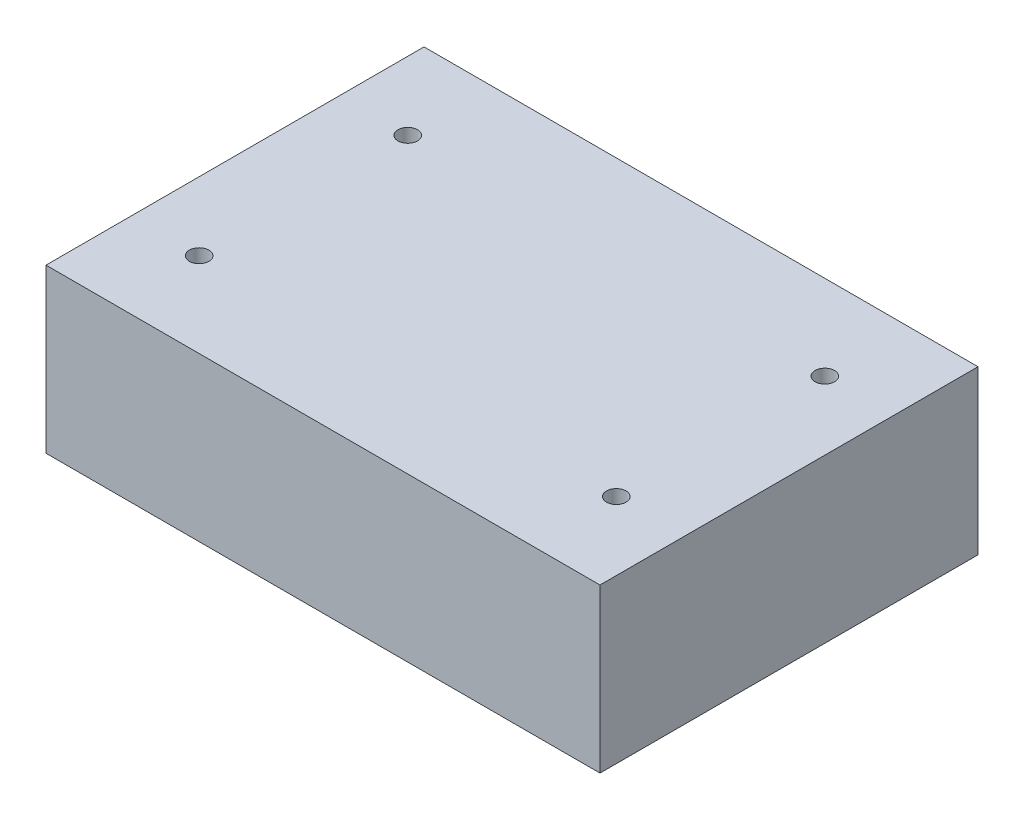
SolidWorks part; units mm, degrees
ref_plane "Front" through (0, 0, 0) normal (0, 0, 1) x (1, 0, 0)
ref_plane "Top" through (0, 0, 0) normal (0, 1, 0) x (1, 0, 0)
ref_plane "Right" through (0, 0, 0) normal (1, 0, 0) x (0, 0, -1)
sketch "Sketch1" plane through (0, 0, 0) normal (0, 1, 0) x (1, 0, 0)
  line L0 (0, 29) -> (85, 29) construction
  line L1 (0, 0) -> (85, 0)
  line L2 (0, 0) -> (0, 58)
  line L3 (0, 58) -> (85, 58)
  line L4 (85, 0) -> (85, 58)
  line L5 (42.5, 58) -> (42.5, 0) construction
  circle A0 centre (10.5, 45) radius 1.5
  circle A1 centre (74.5, 45) radius 1.5
  circle A2 centre (74.5, 13) radius 1.5
  circle A3 centre (10.5, 13) radius 1.5
  dimension "D3" = 3
  dimension "D4" = 32
  dimension "D5" = 64
  dimension "D1" = 85
  dimension "D2" = 58
extrude "Boss-Extrude1" add sketch "Sketch1" along normal blind 25
